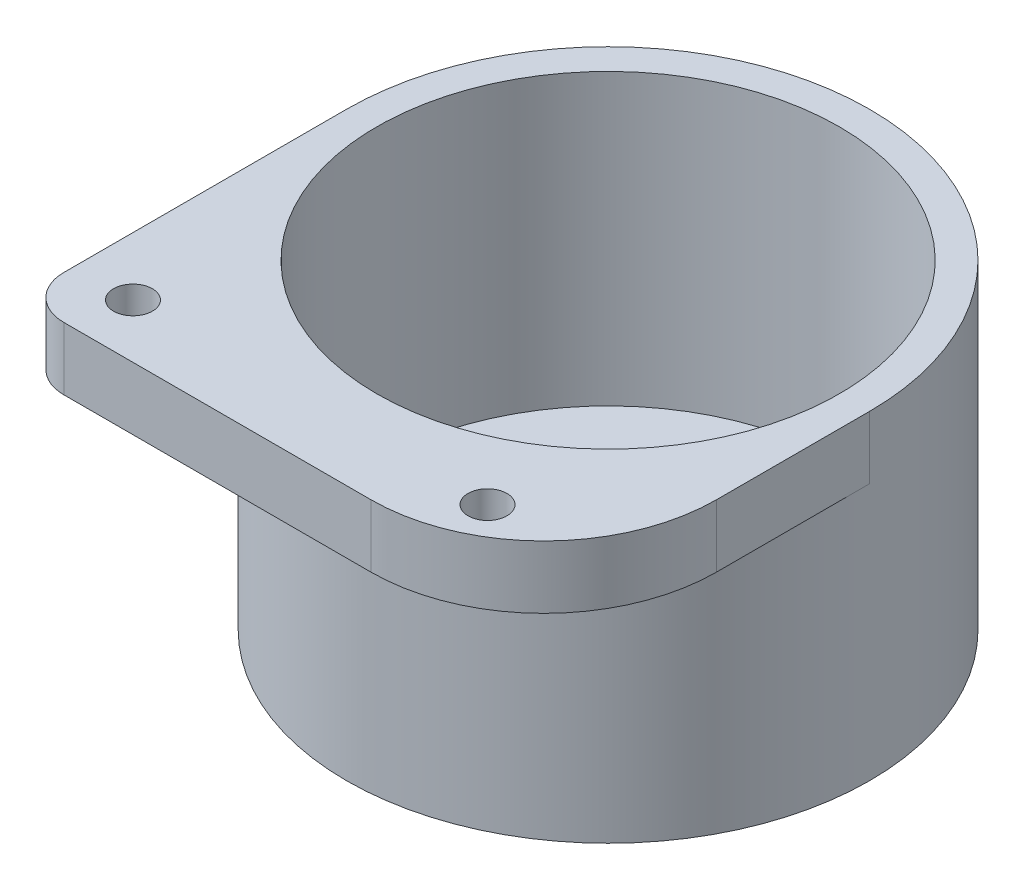
SolidWorks part; units mm, degrees
ref_plane "Спереди" through (0, 0, 0) normal (0, 0, 1) x (1, 0, 0)
ref_plane "Сверху" through (0, 0, 0) normal (0, 1, 0) x (1, 0, 0)
ref_plane "Справа" through (0, 0, 0) normal (1, 0, 0) x (0, 0, -1)
sketch "Эскиз1" plane through (0, 0, 0) normal (0, 1, 0) x (1, 0, 0)
  circle A1 centre (0, 0) radius 60.5
extrude "Бобышка-Вытянуть1" add sketch "Эскиз1" along normal blind 7
sketch "Эскиз2" plane through (0, 7, 0) normal (0, 1, 0) x (1, 0, 0)
  circle A0 centre (0, 0) radius 60.5
  circle A1 centre (0, 0) radius 53.5
  dimension "D1" = 107
extrude "Бобышка-Вытянуть2" add sketch "Эскиз2" along normal blind 67
sketch "Эскиз3" plane through (0, 7, 0) normal (0, 1, 0) x (1, 0, 0)
  circle A0 centre (0, 0) radius 17.75
  dimension "D1" = 35.5
extrude "Вырез-Вытянуть1" cut sketch "Эскиз3" against normal blind 54
sketch "Эскиз6" plane through (0, 74, 0) normal (0, 1, 0) x (1, 0, 0)
  line L0 (-53.5, 0) -> (53.5, 0)
  line L1 (-60.5, 0) -> (60.5, 0)
  line L2 (-60.5, 0) -> (-60.5, -65.3879)
  line L3 (60.5, 0) -> (60.5, -35.3879)
  line L4 (-50.5, -75.3879) -> (20.5, -75.3879)
  line L5 (-42.5, -62.8903) -> (30.5, -62.8903)
  circle A0 centre (0, 0) radius 53.5 construction
  circle A1 centre (0, 0) radius 53.5
  circle A2 centre (0, 0) radius 53.5
  circle A3 centre (0, 0) radius 60.5
  circle A4 centre (-47, -62.8903) radius 4.5
  circle A5 centre (35, -62.8903) radius 4.5
  arc A6 (-60.5, -65.3879) -> (-50.5, -75.3879) centre (-50.5, -65.3879) ccw
  arc A7 (60.5, -35.3879) -> (20.5, -75.3879) centre (20.5, -35.3879) cw
  dimension "D1" = 9
  dimension "D2" = 9
  dimension "D3" = 13.5
  dimension "D6" = 10
  dimension "D7" = 40
  dimension "D4" = 73
  dimension "D5" = 12.4977
extrude "Бобышка-Вытянуть3" add sketch "Эскиз6" against normal blind 14.5
